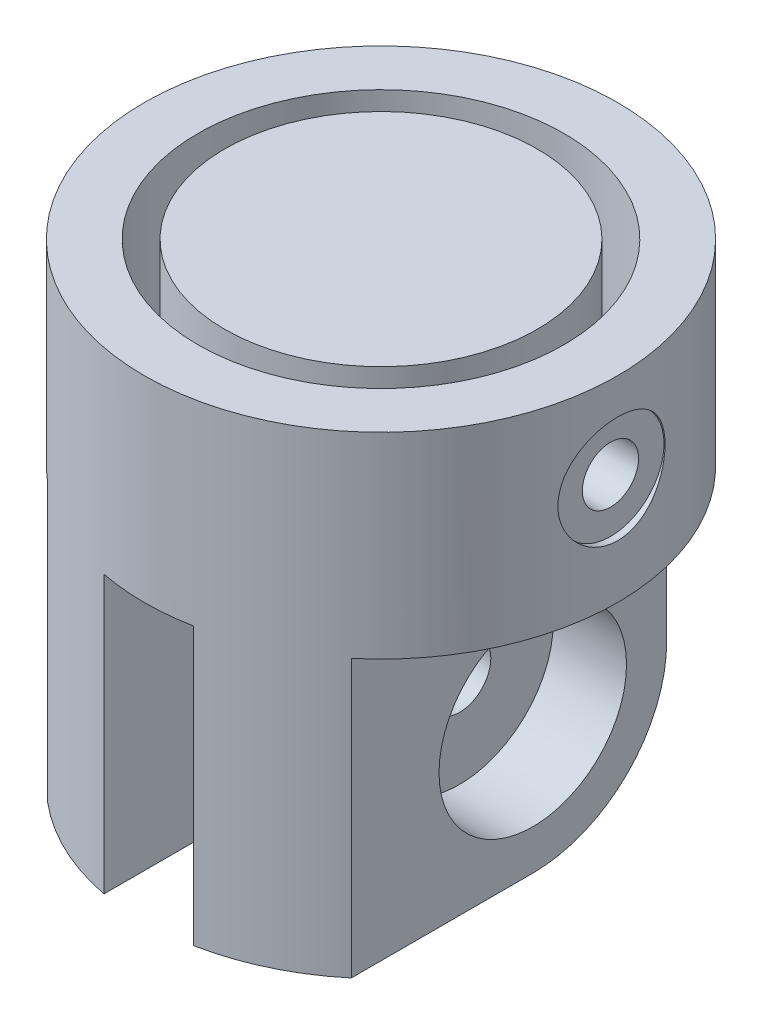
SolidWorks part; units mm, degrees
material "PLA Black"
ref_plane "Front" through (0, 0, 0) normal (0, 0, 1) x (1, 0, 0)
ref_plane "Top" through (0, 0, 0) normal (0, 1, 0) x (1, 0, 0)
ref_plane "Right" through (0, 0, 0) normal (1, 0, 0) x (0, 0, -1)
sketch "Sketch1" plane through (0, 0, 0) normal (0, 1, 0) x (1, 0, 0)
  line L0 (0, 8.75) -> (0, 10.25) construction
  circle A0 centre (0, 0) radius 10.25
  circle A1 centre (0, 0) radius 13.25
  circle A2 centre (0, 0) radius 9.5 construction
  circle A4 centre (0, 0) radius 8.75
  point P11 (0, 9.5)
  dimension "D1" = 1.5
  dimension "D2" = 3
  dimension "D3" = 19
extrude "Boss-Extrude1" add sketch "Sketch1" along normal blind 10
sketch "Sketch3" plane through (0, 0, 0) normal (0, -1, 0) x (1, 0, 0)
  circle A2 centre (0, 0) radius 13.25 construction
  circle A3 centre (0, 0) radius 13.25
extrude "Boss-Extrude2" add sketch "Sketch3" along normal blind 1
sketch "Sketch4" plane through (0, -1, 0) normal (0, -1, 0) x (1, 0, 0)
  line L0 (0, 17.8908) -> (0, -17.0763) construction
  line L2 (2.5, 13.012) -> (2.5, -7.5)
  line L3 (2.5, -7.5) -> (8.5, -7.5)
  line L4 (8.5, 10.1643) -> (8.5, -7.5)
  line L5 (-8.5, 10.1643) -> (-8.5, -7.5)
  line L6 (-2.5, -7.5) -> (-8.5, -7.5)
  line L7 (-2.5, 13.012) -> (-2.5, -7.5)
  line L9 (16.8049, 0) -> (-19.8998, 0) construction
  circle A0 centre (0, 0) radius 13.25 construction
  arc A1 (-2.5, 13.012) -> (-8.5, 10.1643) centre (0, 0) ccw
  arc A2 (8.5, 10.1643) -> (2.5, 13.012) centre (0, 0) ccw
  arc A3 (-13.25, 0) -> (0, -13.25) centre (0, 0) ccw
  circle M1 centre (0, 0) radius 13.25
  dimension "D1" = 6
  dimension "D2" = 5
  dimension "D3" = 7.5
extrude "Boss-Extrude3" add sketch "Sketch4" along normal blind 15.5 contours L7 L5 L6 M1 | L4 L2 L3 M1
sketch "Sketch5" plane through (8.5, 0, 0) normal (1, 0, 0) x (0, 0, -1)
  line L2 (7.5, -9) -> (7.5, -16.5)
  line L3 (7.5, -16.5) -> (0, -16.5)
  line L4 (0, -9) -> (0, -18.9597) construction
  line L5 (-10.1643, -16.5) -> (7.5, -16.5) construction
  line L6 (7.5, -16.5) -> (7.5, -1) construction
  arc A0 (0, -16.5) -> (7.5, -9) centre (0, -9) ccw
  circle A1 centre (0, -9) radius 1.75
  dimension "D1" = 3.5
extrude "Cut-Extrude1" cut sketch "Sketch5" against normal through all both and the other way through all
sketch "Sketch6" plane through (8.5, 0, 0) normal (1, 0, 0) x (0, 0, -1)
  circle A0 centre (0, -9) radius 5.25
  dimension "D1" = 10.5
extrude "Cut-Extrude2" cut sketch "Sketch6" against normal blind 4.1
mirror "Mirror1" about plane through (0, 0, 0) normal (1, 0, 0) of "Cut-Extrude2"
ref_plane "Plane9" through (2.25, 0, 0) normal (1, 0, 0) x (0, 0, -1)
sketch "Sketch7" plane through (2.25, 0, 0) normal (1, 0, 0) x (0, 0, -1)
  line L0 (3.6, -9) -> (3.6, -1) construction
  line L1 (7.5, -1) -> (-10.1643, -1) construction
  line L2 (3.4161, -7.8642) -> (1.1339, -1) construction
  line L3 (2.9196, -6.8938) -> (-1.3321, -1) construction
  line L4 (1.1339, -0.6757) -> (1.1339, -1.4422) construction
  line L5 (2.9659, -6.9596) -> (-1.1339, -1) construction
  line L6 (2.3875, -6.3056) -> (-3.6, -1) construction
  line L8 (0, -1.6788) -> (0, 0) construction
  line L9 (-8.4824, -9) -> (8.712, -9) construction
  line L10 (1.8979, -5.9409) -> (-6.0661, -1) construction
  line L11 (-3.6, -0.3587) -> (-3.6, -1.6788) construction
  circle A0 centre (0, -9) radius 3.6 construction
  dimension "D1" = 7.2
  dimension "D2" = 31.816
  dimension "D3" = 8
ref_plane "Plane1" through (2.25, -1, -3.6) normal (0, 1, 0) x (1, 0, 0)
ref_plane "Plane2" through (2.25, -1, -1.1339) normal (0, 0.9489, 0.3155) x (1, 0, 0)
ref_plane "Plane3" through (2.25, -1, 1.3321) normal (0, 0.811, 0.585) x (1, 0, 0)
ref_plane "Plane5" through (2.25, -1, 1.1339) normal (0, 0.8239, 0.5668) x (1, 0, 0)
ref_plane "Plane6" through (2.25, -1, 3.6) normal (0, 0.6632, 0.7484) x (1, 0, 0)
ref_plane "Plane7" through (2.25, -1, 6.0661) normal (0, 0.5272, 0.8497) x (1, 0, 0)
sketch "Sketch8" plane through (2.25, -1, -3.6) normal (0, 1, 0) x (1, 0, 0)
  circle A0 centre (0, 0) radius 0.825
  dimension "D1" = 1.65
extrude "Cut-Extrude5" cut sketch "Sketch8" along normal blind 5.5 and the other way through all
sketch "Sketch9" plane through (2.25, -1, -1.1339) normal (0, 0.9489, 0.3155) x (1, 0, 0)
  circle A0 centre (0, 0) radius 0.825
  dimension "D1" = 1.65
extrude "Cut-Extrude3" cut sketch "Sketch9" along normal blind 5.5
sketch "Sketch10" plane through (2.25, -1, 1.3321) normal (0, 0.811, 0.585) x (1, 0, 0)
  circle A0 centre (0, 0) radius 0.825
  dimension "D1" = 1.65
sketch "Sketch11" plane through (2.25, -1, 1.1339) normal (0, 0.8239, 0.5668) x (1, 0, 0)
  circle A0 centre (0, 0) radius 0.825
  dimension "D1" = 1.65
sketch "Sketch12" plane through (2.25, -1, 3.6) normal (0, 0.6632, 0.7484) x (1, 0, 0)
  circle A0 centre (0, 0) radius 0.825
  dimension "D1" = 1.65
sketch "Sketch14" plane through (2.25, -1, 6.0661) normal (0, 0.5272, 0.8497) x (1, 0, 0)
  circle A0 centre (0, 0) radius 0.825
  dimension "D1" = 1.65
extrude "Cut-Extrude6" cut sketch "Sketch10" along normal blind 5.5 and the other way through all
extrude "Cut-Extrude7" cut sketch "Sketch11" along normal blind 5.5 and the other way through all contours A0
extrude "Cut-Extrude8" cut sketch "Sketch12" along normal blind 5.5 and the other way through all contours A0
extrude "Cut-Extrude9" cut sketch "Sketch14" along normal blind 5.5 and the other way through all contours A0
ref_plane "Plane8" through (13.25, 0, 0) normal (1, 0, 0) x (0, 0, -1)
hole_wizard "Tap Drill for M3 Helicoil1" positions "Sketch17" profile "Sketch18" hole size "M3x0.5" standard "DIN"
sketch "Sketch17" plane through (13.25, 0, 0) normal (1, 0, 0) x (0, 0, -1)
  line L0 (-22.2973, 5) -> (18.0703, 5) construction
  line L8 (13.25, 10) -> (-13.25, 10) construction
  line L9 (10.25, 0) -> (-10.25, 0) construction
  line L10 (0, 12.9669) -> (0, -1.7456) construction
  point P0 (0, 5)
sketch "Sketch18" plane through (13.25, 5, 0) normal (0, 1, 0) x (0, 0, -1)
  line L0 (0, 0) -> (0, 6.9464)
  line L1 (0, 6.9464) -> (1.575, 6)
  line L2 (1.575, 6) -> (1.575, 0)
  line L5 (1.575, 0) -> (0, 0)
  line L10 (0, 6.9464) -> (-1.575, 6) construction
  line L11 (0, -6.35) -> (0, 107.95) construction
  dimension "Hole Dia." = 3.15
  dimension "Hole Depth" = 6
  dimension "Drill Angle" = 118
sketch "Sketch20" plane through (13.25, 0, 0) normal (1, 0, 0) x (0, 0, -1)
  circle A0 centre (0, 5) radius 3
  dimension "D1" = 6
extrude "Cut-Extrude10" cut sketch "Sketch20" against normal blind 0.4
mirror "Mirror2" about plane through (0, 0, 0) normal (1, 0, 0) of "Cut-Extrude10", "Tap Drill for M3 Helicoil1"
equation "\"knee_angle\"= 70"
equation "\"ankle_angle\" = 70"
equation "\"hip_angle\" = 30"
equation "\"spring_ankle_parallel_arm_diameter\"= 1.5"
equation "\"spring_ankle_parallel_arm_length\"= 13"
equation "\"spring_ankle_parallel_intern_diameter\"= 5.7"
equation "\"spring_ankle_parallel_angle\"= \"ankle_angle\""
equation "\"spring_ankle_parallel_turns\"= 3"
equation "\"spring_ankle_parallel_pitch\"= \"spring_ankle_parallel_arm_diameter\" * 1.01"
equation "\"spring_ankle_parallel_cutting_distance\"= (1-\"spring_ankle_parallel_angle\" / 360) * \"spring_ankle_parallel_pitch\""
equation "\"spring_ankle_serial_arm_diameter\"= 1.91"
equation "\"spring_ankle_serial_arm_length\"= 10"
equation "\"spring_ankle_serial_intern_diameter\"= 5.7"
equation "\"spring_ankle_serial_angle\"= \"90\""
equation "\"spring_ankle_serial_turns\"= 3"
equation "\"spring_ankle_serial_pitch\"= \"spring_ankle_serial_arm_diameter\" * 1.01"
equation "\"spring_ankle_serial_cutting_distance\"= (1-\"spring_ankle_serial_angle\" / 360) * \"spring_ankle_serial_pitch\""
equation "\"spring_knee_parallel_arm_diameter\"= 1.5"
equation "\"spring_knee_parallel_arm_length\"= 13"
equation "\"spring_knee_parallel_intern_diameter\"= 5.7"
equation "\"spring_knee_parallel_angle\"= -\"knee_angle\" + 90"
equation "\"spring_knee_parallel_turns\"= 3"
equation "\"spring_knee_parallel_pitch\"= \"spring_knee_parallel_arm_diameter\" * 1.01"
equation "\"spring_knee_parallel_cutting_distance\"= (1-(\"spring_knee_parallel_angle\") / 360) * \"spring_knee_parallel_pitch\""
equation "\"spring_knee_serial_arm_diameter\"= 1.91"
equation "\"spring_knee_serial_arm_length\"= 10"
equation "\"spring_knee_serial_intern_diameter\"= 5.7"
equation "\"spring_knee_serial_angle\"= \"90\""
equation "\"spring_knee_serial_turns\"= 3"
equation "\"spring_knee_serial_pitch\"= \"spring_knee_serial_arm_diameter\" * 1.01"
equation "\"spring_knee_serial_cutting_distance\"= (1-\"spring_knee_serial_angle\" / 360) * \"spring_knee_serial_pitch\""
equation "\"spring_ankle_parallel_nominal_diameter\"= \"spring_ankle_parallel_arm_diameter\" + \"spring_ankle_parallel_intern_diameter\""
equation "\"spring_ankle_serial_nominal_diameter\"= \"spring_ankle_serial_arm_diameter\" + \"spring_ankle_serial_intern_diameter\""
equation "\"spring_knee_parallel_nominal_diameter\"= \"spring_knee_parallel_arm_diameter\" + \"spring_knee_parallel_intern_diameter\""
equation "\"spring_knee_serial_nominal_diameter\"= \"spring_knee_serial_arm_diameter\" + \"spring_knee_serial_intern_diameter\""
equation "\"D1@Sketch7\"=\"spring_knee_parallel_nominal_diameter\""
equation "\"D1@Sketch8\"=\"spring_knee_parallel_arm_diameter\"*1.1"
equation "\"D1@Sketch9\"=\"spring_ankle_parallel_arm_diameter\"*1.1"
equation "\"D1@Sketch10\"=\"spring_ankle_parallel_arm_diameter\"*1.1"
equation "\"D1@Sketch11\"=\"spring_ankle_parallel_arm_diameter\"*1.1"
equation "\"D1@Sketch12\"=\"spring_ankle_parallel_arm_diameter\"*1.1"
equation "\"D1@Sketch14\"=\"spring_ankle_parallel_arm_diameter\"*1.1"
equation "\"D1@Cut-Extrude3\"=\"spring_ankle_parallel_arm_length\"-\"axis_structure_distance\""
equation "\"axis_structure_distance\"= 7.5"
equation "\"D1@Cut-Extrude5\"=\"spring_knee_parallel_arm_length\"-\"axis_structure_distance\""
equation "\"D1@Cut-Extrude6\"=\"spring_ankle_parallel_arm_length\"-\"axis_structure_distance\""
equation "\"D1@Cut-Extrude7\"=\"spring_ankle_parallel_arm_length\"-\"axis_structure_distance\""
equation "\"D1@Cut-Extrude8\"=\"spring_ankle_parallel_arm_length\"-\"axis_structure_distance\""
equation "\"D1@Cut-Extrude9\"=\"spring_ankle_parallel_arm_length\"-\"axis_structure_distance\""
equation "\"ankle_angle_max\" = 120"
equation "\"ankle_angle_min\" = 50"
equation "\"knee_angle_max\" = 120"
equation "\"knee_angle_min\" = 0"
equation "\"hip_angle_max\" = 90"
equation "\"hip_angle_min\" = -60"
equation "\"D1@Plane9\"=(\"spring_ankle_parallel_arm_diameter\"*\"spring_ankle_parallel_turns\")/2"
